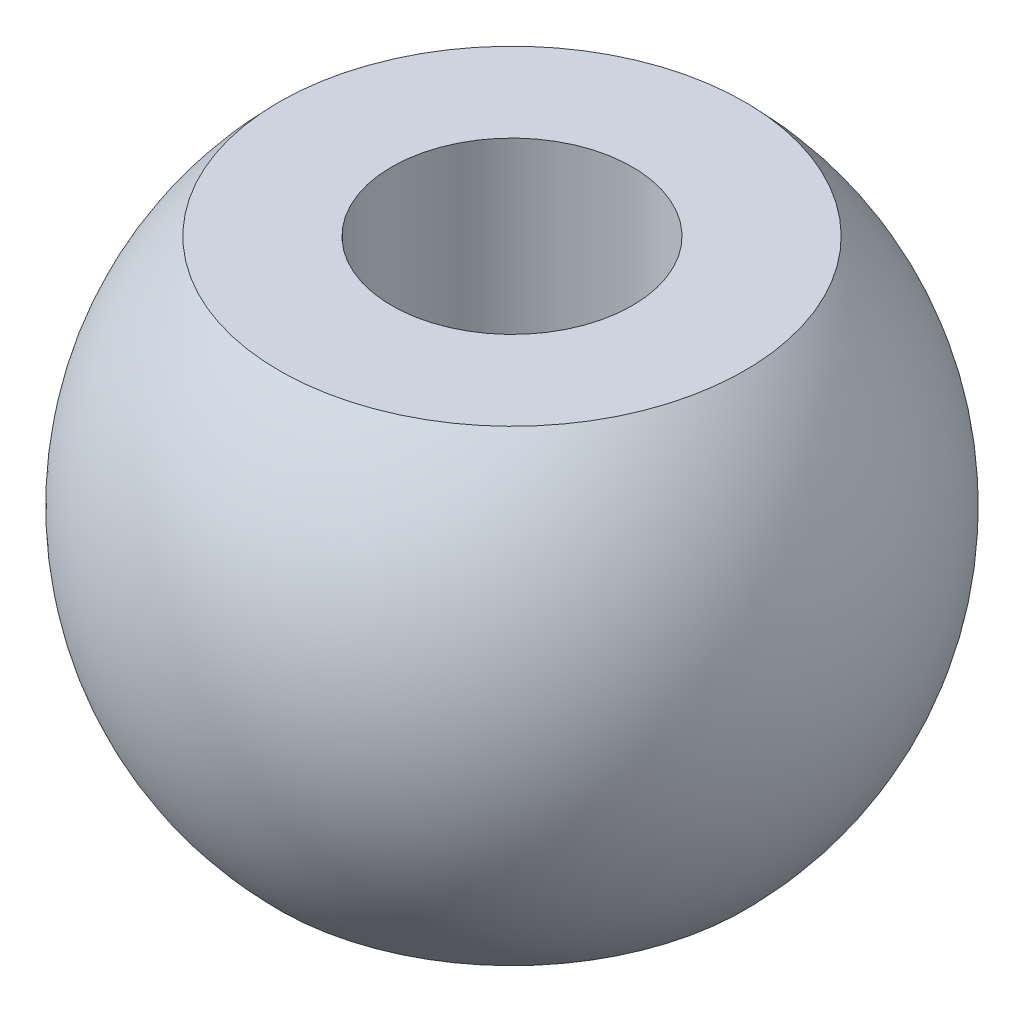
SolidWorks part; units mm, degrees
ref_plane "Front Plane" through (0, 0, 0) normal (0, 0, 1) x (1, 0, 0)
ref_plane "Top Plane" through (0, 0, 0) normal (0, 1, 0) x (1, 0, 0)
ref_plane "Right Plane" through (0, 0, 0) normal (1, 0, 0) x (0, 0, -1)
sketch "Sketch1" plane through (0, 0, 0) normal (0, 0, 1) x (1, 0, 0)
  line L0 (0, 6.0208) -> (0, -6.0208)
  line L1 (0, 6.0208) -> (-6, 6.0208)
  line L2 (-6, -6.0208) -> (0, -6.0208)
  arc A0 (-6, 6.0208) -> (-6, -6.0208) centre (0, 0) ccw
  point P8 (0, 0)
  dimension "D1" = 17
  dimension "D2" = 6
  dimension "D3" = 12.0416
revolve "Revolve2" add sketch "Sketch1" angle 360 about L0
sketch "Sketch3" plane through (0, 6.0208, 0) normal (0, 1, 0) x (1, 0, 0)
  circle A0 centre (0, 0) radius 3.1
  dimension "D1" = 6.2
extrude "Cut-Extrude1" cut sketch "Sketch3" against normal through all
